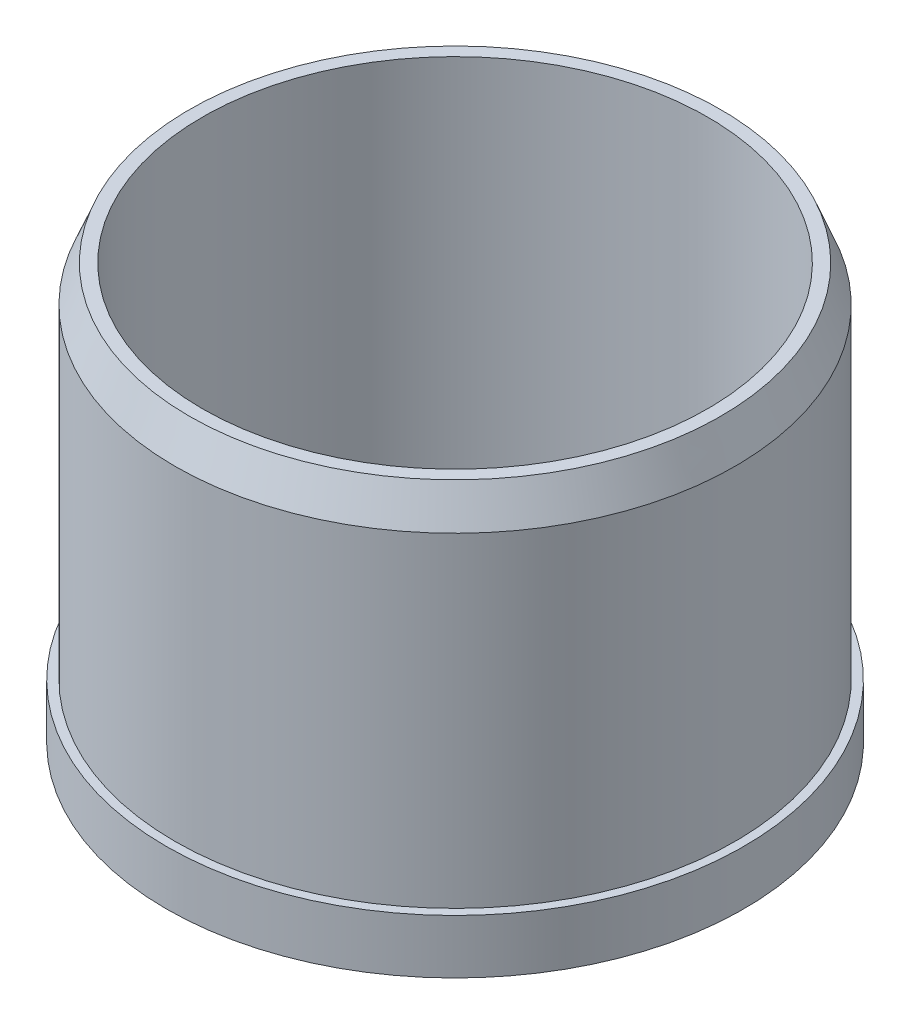
SolidWorks part; units mm, degrees
material "ABS"
ref_plane "Front Plane" through (0, 0, 0) normal (0, 0, 1) x (1, 0, 0)
ref_plane "Top Plane" through (0, 0, 0) normal (0, 1, 0) x (1, 0, 0)
ref_plane "Right Plane" through (0, 0, 0) normal (1, 0, 0) x (0, 0, -1)
sketch "Sketch1" plane through (0, 0, 0) normal (0, 1, 0) x (1, 0, 0)
  line L0 (0, 0) -> (7.1, 0)
  line L1 (7.1, 0) -> (9.6, 0)
  line L2 (9.6, 0) -> (9.6, 2.5)
  line L3 (9.6, 2.5) -> (6.6453, 2.5)
  line L4 (9.6, 0) -> (9.6, -2.5)
  line L5 (9.6, -2.5) -> (6.6453, -2.5)
  line L6 (0, 12.7) -> (0, 44.45)
  circle A0 centre (0, 0) radius 50.8
  circle A1 centre (0, 0) radius 7.1
  circle A2 centre (0, 0) radius 12.7
  circle A3 centre (0, 0) radius 44.45
  circle A4 centre (0, 28.575) radius 12.7
  circle A5 centre (27.1764, 8.8302) radius 12.7
  circle A6 centre (16.796, -23.1177) radius 12.7
  circle A7 centre (-16.796, -23.1177) radius 12.7
  circle A8 centre (-27.1764, 8.8302) radius 12.7
  point P26 (0, 0)
  dimension "D1" = 101.6
  dimension "D2" = 14.2
  dimension "D6" = 25.4
  dimension "D7" = 88.9
  dimension "D8" = 25.4
  dimension "D3" = 2.5
  dimension "D4" = 2.5
  dimension "D5" = 2.5
  dimension "D9" = 5
extrude "Boss-Extrude1" add sketch "Sketch1" along normal blind 9.525
sketch "Sketch2" plane through (0, 9.525, 0) normal (0, 1, 0) x (1, 0, 0)
  circle A0 centre (0, 0) radius 49.276
  circle A1 centre (0, 0) radius 44.45
  dimension "D1" = 98.552
  dimension "D2" = 88.9
extrude "Boss-Extrude2" add sketch "Sketch2" along normal blind 63.5
sketch "Sketch3" plane through (0, 9.525, 0) normal (0, 1, 0) x (1, 0, 0)
  line L0 (6.6453, 2.5) -> (9.6, 2.5)
  line L1 (9.6, 2.5) -> (9.6, -2.5)
  line L2 (9.6, -2.5) -> (6.6453, -2.5)
  circle A0 centre (0, 0) radius 12.7
  circle A2 centre (0, 0) radius 7.1
  arc M5 (6.6453, -2.5) -> (6.6453, 2.5) centre (0, 0) cw
  line M6 (6.6453, 2.5) -> (9.6, 2.5)
  line M7 (9.6, 2.5) -> (9.6, -2.5)
  line M8 (9.6, -2.5) -> (6.6453, -2.5)
  dimension "D1" = 25.4
  dimension "D2" = 14.2
extrude "Boss-Extrude3" add sketch "Sketch3" along normal blind 15.875 contours A0 M8 M5 M6 M7
chamfer "Chamfer1" distance 6.35 distance2 2.54 1 edges at (0, 73.025, 49.276)
sketch "Sketch4" plane through (0, 25.4, 0) normal (0, 1, 0) x (1, 0, 0)
  circle A0 centre (0, 0) radius 12.7
  dimension "D1" = 25.4
extrude "Boss-Extrude4" add sketch "Sketch4" along normal blind 6.35
fillet "Fillet1" radius 2.54 1 edges at (0, 31.75, 12.7)
